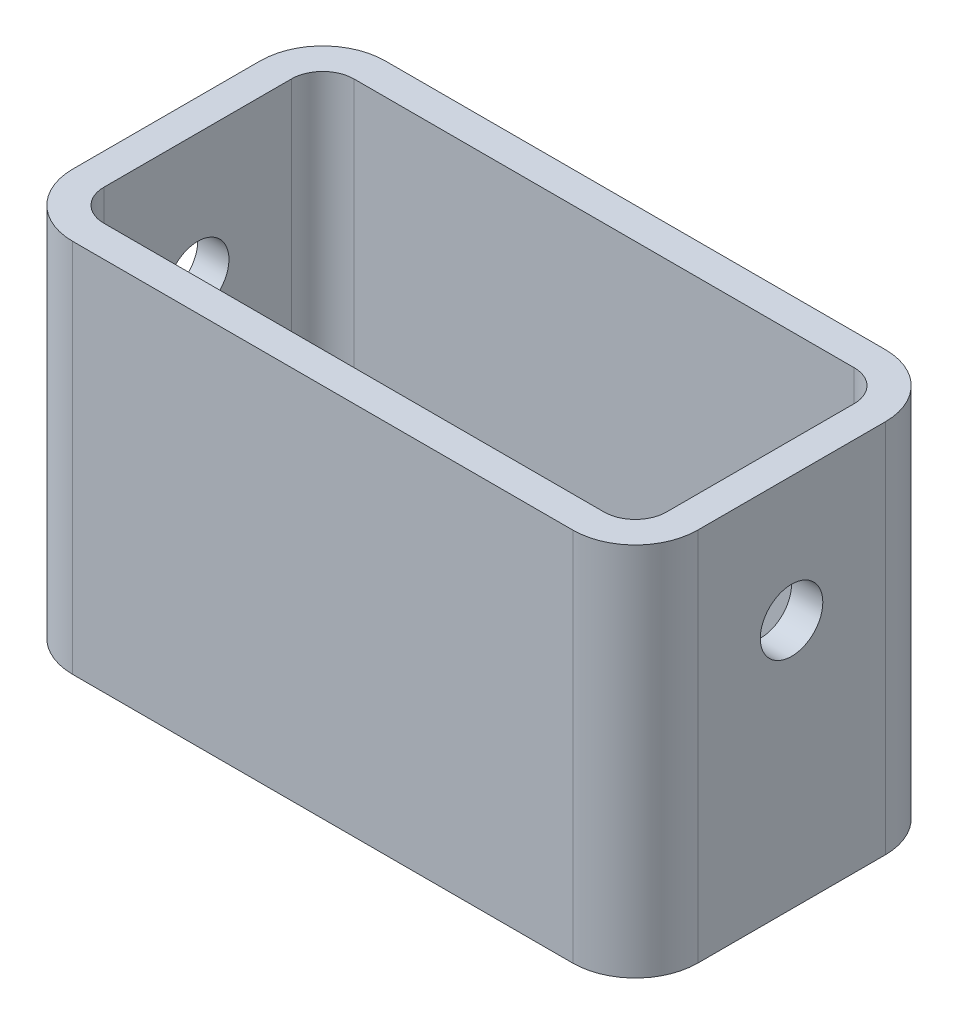
SolidWorks part; units mm, degrees
ref_plane "Front" through (0, 0, 0) normal (0, 0, 1) x (1, 0, 0)
ref_plane "Top" through (0, 0, 0) normal (0, 1, 0) x (1, 0, 0)
ref_plane "Right" through (0, 0, 0) normal (1, 0, 0) x (0, 0, -1)
sketch "Sketch1" plane through (0, 0, 0) normal (0, 0, 1) x (1, 0, 0)
  line L1 (-134.4641, -122.648) -> (-34.4641, -122.648)
  line L2 (-134.4641, -122.648) -> (-134.4641, -62.648)
  line L3 (-134.4641, -62.648) -> (-34.4641, -62.648)
  line L4 (-34.4641, -122.648) -> (-34.4641, -62.648)
  dimension "D1" = 100
  dimension "D2" = 60
extrude "Boss-Extrude1" add sketch "Sketch1" along normal blind 50
fillet "Fillet1" radius 10 4 edges at (-34.4641, -92.648, 0) (-134.4641, -92.648, 0) (-134.4641, -92.648, 50) (-34.4641, -92.648, 50)
shell "Shell1" thickness 5
sketch "Sketch3" plane through (-34.4641, 0, 0) normal (1, 0, 0) x (0, 0, -1)
  line L1 (-10, -122.648) -> (0, -122.648) construction
  line L3 (-50, -122.648) -> (-50, -62.648) construction
  circle A0 centre (-25, -82.648) radius 5
  dimension "D1" = 10
  dimension "D2" = 25
  dimension "D3" = 40
extrude "Cut-Extrude1" cut sketch "Sketch3" against normal through all
